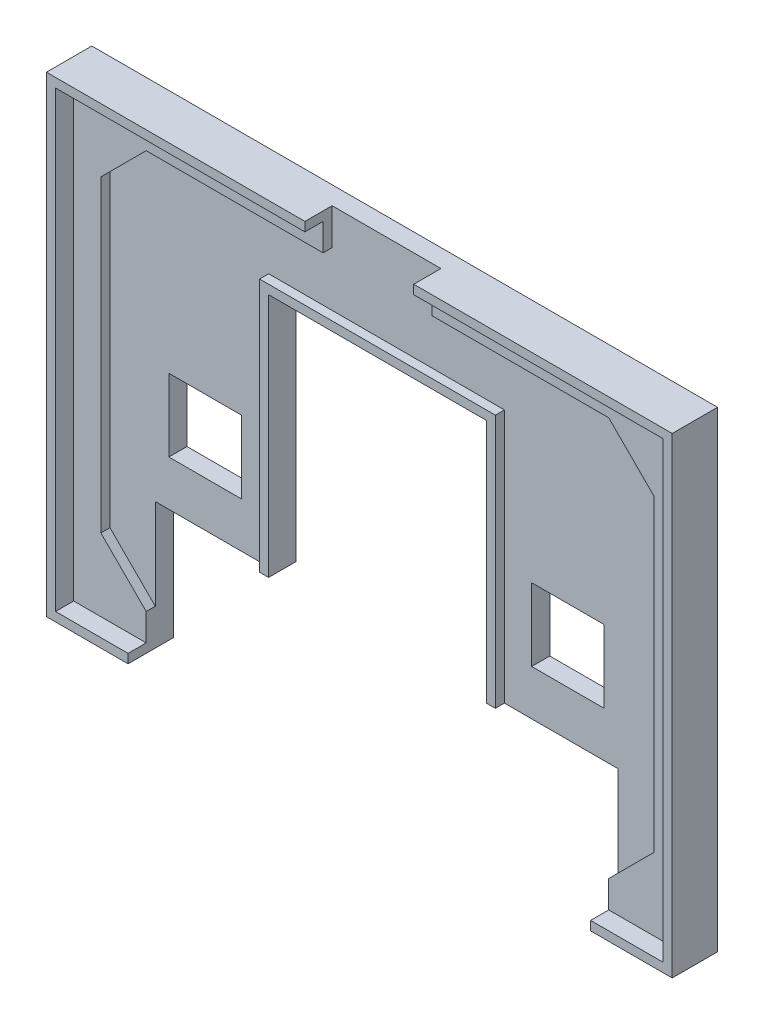
SolidWorks part; units mm, degrees
ref_plane "Přední rovina" through (0, 0, 0) normal (0, 0, 1) x (1, 0, 0)
ref_plane "Horní rovina" through (0, 0, 0) normal (0, 1, 0) x (1, 0, 0)
ref_plane "Pravá rovina" through (0, 0, 0) normal (1, 0, 0) x (0, 0, -1)
sketch "Skica1" plane through (0, 0, 0) normal (0, 0, 1) x (1, 0, 0)
  line L1 (-33.5, -25) -> (33.5, -25)
  line L2 (-33.5, -25) -> (-33.5, 25)
  line L3 (-33.5, 25) -> (33.5, 25)
  line L4 (33.5, -25) -> (33.5, 25)
  line L5 (-33.5, -25) -> (33.5, 25) construction
  line L6 (-33.5, 25) -> (33.5, -25) construction
  point P0 (0, 0)
  dimension "D1" = 67
  dimension "D2" = 50
extrude "Přidat vysunutím1" add sketch "Skica1" along normal blind 3
sketch "Skica2" plane through (0, 0, 3) normal (0, 0, 1) x (1, 0, 0)
  line L0 (-1000, 0) -> (49000, 0) construction
  line L1 (0, -1000) -> (0, 49000) construction
  line L2 (-1000, -22) -> (49000, -22) construction
  line L3 (-25.5, -1000) -> (-25.5, 49000) construction
  line L4 (-30.5, -1000) -> (-30.5, 49000) construction
  line L6 (-33.5, -25) -> (33.5, -25) construction
  line L7 (-25.5, -22) -> (-30.5, -17)
  line L8 (-30.5, -17) -> (-30.5, 17)
  line L9 (-25.5, -22) -> (25.5, -22)
  line L10 (30.5, -17) -> (30.5, 17)
  line L11 (25.5, -22) -> (30.5, -17)
  line L12 (25.5, 22) -> (30.5, 17)
  line L13 (-25.5, 22) -> (25.5, 22)
  line L14 (-25.5, 22) -> (-30.5, 17)
  point P20 (0, -22)
  point P21 (30.5, 0)
  point P24 (-30.5, 0)
  dimension "D1" = 30.5
  dimension "D2" = 5
  dimension "D3" = 3
  dimension "D4" = 45
extrude "Odebrat vysunutím1" cut sketch "Skica2" against normal offset from surface (1 mm away) 2 up to face at (0, 0, 0)
sketch "Skica3" plane through (0, 0, 0) normal (0, 0, -1) x (-1, 0, 0)
  line L0 (0, -1000) -> (0, 49000) construction
  line L1 (33.5, -25) -> (-33.5, -25) construction
  line L2 (24, 1) -> (16, 1)
  line L3 (24, 1) -> (24, -7)
  line L4 (24, -7) -> (16, -7)
  line L5 (16, 1) -> (16, -7)
  line L6 (-16, 1) -> (-16, -7)
  line L7 (33.5, -25) -> (-33.5, -25) construction
  line L8 (25.5, -25) -> (-25.5, -25)
  line L9 (25.5, -25) -> (25.5, -12)
  line L11 (-25.5, -25) -> (-25.5, -12)
  line L12 (-24, -7) -> (-16, -7)
  line L13 (25.5, -12) -> (12, -12)
  line L15 (12, -12) -> (12, 15)
  line L16 (12, 15) -> (-12, 15)
  line L17 (-12, -12) -> (-12, 15)
  line L18 (-12, -12) -> (-25.5, -12)
  line L19 (-24, 1) -> (-24, -7)
  line L20 (-24, 1) -> (-16, 1)
  dimension "D1" = 16
  dimension "D2" = 8
  dimension "D3" = 18
  dimension "D4" = 13
  dimension "D5" = 51
  dimension "D6" = 24
  dimension "D7" = 27
extrude "Odebrat vysunutím2" cut sketch "Skica3" against normal through all
sketch "Skica4" plane through (0, 0, 2) normal (0, 0, 1) x (1, 0, 0)
  line L0 (12, 15) -> (12, -12) construction
  line L1 (-12, -12) -> (-12, 15) construction
  line L2 (-12, 15) -> (12, 15) construction
  line L3 (12, 15) -> (12, -12)
  line L4 (-12, -12) -> (-12, 15)
  line L5 (-12, 15) -> (12, 15)
extrude "Vysunout tenkostěnný1" add sketch "Skica4" along normal up to surface (1 mm away) thin up to face at (0, -3.5714, 3) thin type one direction reverse wall 1
sketch "Skica5" plane through (0, 0, 0) normal (0, 0, -1) x (-1, 0, 0)
  line L0 (-33.5, 25) -> (33.5, 25) construction
  line L1 (33.5, 25) -> (33.5, -25) construction
  line L2 (33.5, -25) -> (25.5, -25) construction
  line L3 (-33.5, -25) -> (-33.5, 25) construction
  line L4 (-25.5, -25) -> (-33.5, -25) construction
  line L5 (-33.5, 25) -> (33.5, 25)
  line L6 (33.5, 25) -> (33.5, -25)
  line L7 (33.5, -25) -> (25.5, -25)
  line L8 (-33.5, -25) -> (-33.5, 25)
  line L9 (-25.5, -25) -> (-33.5, -25)
extrude "Vysunout tenkostěnný2" add sketch "Skica5" against normal blind 5 thin thin type one direction reverse wall 1
sketch "Skica6" plane through (0, 0, 2) normal (0, 0, 1) x (1, 0, 0)
  line L0 (0, -1000) -> (0, 49000) construction
  line L1 (25.5, 22) -> (-25.5, 22) construction
  line L2 (-6, 22) -> (6, 22)
  line L3 (-6, 22) -> (-6, 26)
  line L4 (-6, 26) -> (6, 26)
  line L5 (6, 22) -> (6, 26)
  line L6 (34.5, 26) -> (-34.5, 26) construction
  dimension "D1" = 12
extrude "Odebrat vysunutím3" cut sketch "Skica6" along normal through all
sketch "Skica8" plane through (0, 0, 0) normal (0, 0, -1) x (-1, 0, 0)
  line L0 (-28.7522, 22) -> (-27.75, 22)
  line L1 (-27.75, 22) -> (-27.75, 21)
  line L2 (-27.75, 21) -> (-26.75, 21)
  line L3 (-26.75, 21) -> (-26.75, 20)
  line L4 (-26.75, 20) -> (-25.75, 20)
  line L5 (-25.75, 20) -> (-25.75, 19)
  line L7 (-20.75, 19) -> (-20.75, 20)
  line L8 (-20.75, 20) -> (-19.75, 20)
  line L9 (-19.75, 20) -> (-19.75, 21)
  line L10 (-19.75, 21) -> (-18.75, 21)
  line L11 (-18.75, 21) -> (-18.75, 22)
  line L12 (-18.75, 22) -> (-17.75, 22)
  line L13 (-17.75, 22) -> (-17.75, 21)
  line L14 (-17.75, 21) -> (-16.75, 21)
  line L15 (-16.75, 21) -> (-16.75, 19)
  line L16 (-16.75, 19) -> (-15.75, 19)
  line L17 (-15.75, 19) -> (-15.75, 15)
  line L18 (-15.75, 15) -> (-14.75, 15)
  line L19 (-14.75, 15) -> (-14.75, 11)
  line L20 (-14.75, 11) -> (-15.75, 11)
  line L21 (-15.75, 11) -> (-15.75, 10)
  line L22 (-15.75, 10) -> (-16.75, 10)
  line L23 (-16.75, 10) -> (-16.75, 9)
  line L24 (-16.75, 9) -> (-17.75, 9)
  line L25 (-17.75, 9) -> (-17.75, 8)
  line L26 (-17.75, 8) -> (-18.75, 8)
  line L27 (-18.75, 8) -> (-18.75, 7)
  line L28 (-18.75, 7) -> (-27.7522, 7)
  line L29 (-27.7522, 7) -> (-27.7522, 8)
  line L30 (-27.7522, 8) -> (-28.7522, 8)
  line L31 (-28.7522, 8) -> (-28.7522, 9)
  line L32 (-28.7522, 9) -> (-29.7522, 9)
  line L33 (-29.7522, 9) -> (-29.7522, 10)
  line L34 (-29.7522, 10) -> (-30.7522, 10)
  line L35 (-30.7522, 10) -> (-30.7522, 11)
  line L36 (-30.7522, 11) -> (-31.7522, 11)
  line L37 (-31.7522, 11) -> (-31.7522, 15)
  line L38 (-31.7522, 15) -> (-30.7522, 15)
  line L39 (-30.7522, 15) -> (-30.7522, 19)
  line L40 (-30.7522, 19) -> (-29.7522, 19)
  line L41 (-29.7522, 19) -> (-29.7522, 21)
  line L42 (-29.7522, 21) -> (-28.7522, 21)
  line L43 (-28.7522, 21) -> (-28.7522, 22)
  line L44 (-25.75, 19) -> (-20.75, 19)
  line L45 (-12, 15) -> (-12, -12) construction
  line L47 (-34.5, 26) -> (34.5, 26) construction
  line L48 (0, 0) -> (0, 28.5236) construction
  line L49 (25.75, 19) -> (20.75, 19)
  line L50 (25.75, 20) -> (25.75, 19)
  line L51 (26.75, 20) -> (25.75, 20)
  line L52 (26.75, 21) -> (26.75, 20)
  line L53 (27.75, 21) -> (26.75, 21)
  line L54 (27.75, 22) -> (27.75, 21)
  line L55 (28.7522, 22) -> (27.75, 22)
  line L56 (28.7522, 21) -> (28.7522, 22)
  line L57 (29.7522, 21) -> (28.7522, 21)
  line L58 (29.7522, 19) -> (29.7522, 21)
  line L59 (30.7522, 19) -> (29.7522, 19)
  line L60 (30.7522, 15) -> (30.7522, 19)
  line L61 (31.7522, 15) -> (30.7522, 15)
  line L62 (31.7522, 11) -> (31.7522, 15)
  line L63 (30.7522, 11) -> (31.7522, 11)
  line L64 (30.7522, 10) -> (30.7522, 11)
  line L65 (29.7522, 10) -> (30.7522, 10)
  line L66 (29.7522, 9) -> (29.7522, 10)
  line L67 (28.7522, 9) -> (29.7522, 9)
  line L68 (28.7522, 8) -> (28.7522, 9)
  line L69 (27.7522, 8) -> (28.7522, 8)
  line L70 (27.7522, 7) -> (27.7522, 8)
  line L71 (18.75, 7) -> (27.7522, 7)
  line L72 (18.75, 8) -> (18.75, 7)
  line L73 (17.75, 8) -> (18.75, 8)
  line L74 (17.75, 9) -> (17.75, 8)
  line L75 (16.75, 9) -> (17.75, 9)
  line L76 (16.75, 10) -> (16.75, 9)
  line L77 (15.75, 10) -> (16.75, 10)
  line L78 (15.75, 11) -> (15.75, 10)
  line L79 (14.75, 11) -> (15.75, 11)
  line L80 (14.75, 15) -> (14.75, 11)
  line L81 (15.75, 15) -> (14.75, 15)
  line L82 (15.75, 19) -> (15.75, 15)
  line L83 (16.75, 19) -> (15.75, 19)
  line L84 (16.75, 21) -> (16.75, 19)
  line L85 (17.75, 21) -> (16.75, 21)
  line L86 (17.75, 22) -> (17.75, 21)
  line L87 (18.75, 22) -> (17.75, 22)
  line L88 (18.75, 21) -> (18.75, 22)
  line L89 (19.75, 21) -> (18.75, 21)
  line L90 (19.75, 20) -> (19.75, 21)
  line L91 (20.75, 20) -> (19.75, 20)
  line L92 (20.75, 19) -> (20.75, 20)
  dimension "D1" = 1.0022
  dimension "D2" = 1
  dimension "D3" = 1
  dimension "D4" = 1
  dimension "D5" = 1
  dimension "D6" = 1
  dimension "D7" = 1
  dimension "D8" = 1
  dimension "D9" = 1
  dimension "D10" = 1
  dimension "D11" = 1
  dimension "D12" = 1
  dimension "D13" = 1
  dimension "D14" = 1
  dimension "D15" = 1
  dimension "D16" = 1
  dimension "D17" = 1
  dimension "D18" = 1
  dimension "D19" = 2
  dimension "D20" = 5
  dimension "D21" = 4
  dimension "D22" = 4
  dimension "D23" = 4
  dimension "D24" = 4
  dimension "D25" = 1
  dimension "D26" = 1
  dimension "D27" = 1
  dimension "D28" = 1
  dimension "D29" = 1
  dimension "D30" = 1
  dimension "D31" = 1
  dimension "D32" = 1
  dimension "D33" = 1
  dimension "D34" = 1
  dimension "D35" = 1
  dimension "D36" = 1
  dimension "D37" = 1
  dimension "D38" = 1
  dimension "D39" = 1
  dimension "D40" = 1
  dimension "D41" = 1
  dimension "D42" = 2.75
  dimension "D43" = 4
extrude "Odebrat vysunutím4" cut sketch "Skica8" against normal blind 1
sketch "Skica9" plane through (0, 0, 0) normal (0, 0, -1) x (-1, 0, 0)
  line L0 (-30.7522, 15) -> (-31.7522, 15) construction
  line L1 (-27.75, 14) -> (-25.75, 14)
  line L2 (-27.75, 14) -> (-27.75, 12)
  line L3 (-27.75, 12) -> (-25.75, 12)
  line L4 (-25.75, 14) -> (-25.75, 12)
  line L5 (-21.75, 10) -> (-21.75, 9)
  line L6 (-23.25, 19) -> (-23.25, 4.92) construction
  line L7 (-20.75, 19) -> (-25.75, 19) construction
  line L8 (-18.75, 12) -> (-20.75, 12)
  line L9 (-20.75, 14) -> (-20.75, 12)
  line L10 (-18.75, 14) -> (-20.75, 14)
  line L11 (-18.75, 14) -> (-18.75, 12)
  line L12 (-23.75, 12) -> (-22.75, 12)
  line L13 (-22.75, 12) -> (-22.75, 10)
  line L14 (-22.75, 10) -> (-21.75, 10)
  line L15 (-21.75, 9) -> (-24.75, 9)
  line L16 (-24.75, 9) -> (-24.75, 10)
  line L17 (-24.75, 10) -> (-23.75, 10)
  line L18 (-23.75, 10) -> (-23.75, 12)
  line L19 (0, 0) -> (0, 33.5066) construction
  line L20 (-25.75, 19) -> (-25.75, 20) construction
  line L22 (24.75, 10) -> (23.75, 10)
  line L23 (24.75, 9) -> (24.75, 10)
  line L24 (21.75, 9) -> (24.75, 9)
  line L25 (21.75, 10) -> (21.75, 9)
  line L26 (22.75, 10) -> (21.75, 10)
  line L27 (22.75, 12) -> (22.75, 10)
  line L28 (23.75, 12) -> (22.75, 12)
  line L29 (23.75, 10) -> (23.75, 12)
  line L30 (18.75, 14) -> (18.75, 12)
  line L31 (18.75, 14) -> (20.75, 14)
  line L32 (20.75, 14) -> (20.75, 12)
  line L33 (18.75, 12) -> (20.75, 12)
  line L34 (27.75, 12) -> (25.75, 12)
  line L35 (25.75, 14) -> (25.75, 12)
  line L36 (27.75, 14) -> (25.75, 14)
  line L37 (27.75, 14) -> (27.75, 12)
  dimension "D1" = 2
  dimension "D2" = 3
  dimension "D3" = 1
  dimension "D4" = 1
  dimension "D5" = 1
  dimension "D6" = 2
  dimension "D7" = 2
  dimension "D8" = 1
  dimension "D9" = 2
  dimension "D10" = 0
extrude "Přidat vysunutím2" add sketch "Skica9" along normal blind 1 from offset 1 offset against normal yes
sketch "Skica11" plane through (0, 0, 0) normal (0, 0, -1) x (-1, 0, 0)
  line L0 (-21.75, 10) -> (-22.75, 10) construction
  line L1 (-21.75, 11) -> (-20.75, 11)
  line L2 (-21.75, 11) -> (-21.75, 10)
  line L3 (-21.75, 10) -> (-20.75, 10)
  line L4 (-20.75, 11) -> (-20.75, 10)
  line L5 (-21.75, 9) -> (-21.75, 10) construction
  line L6 (-23.2511, 7) -> (-23.2511, 16.4685) construction
  line L7 (-27.7522, 7) -> (-18.75, 7) construction
  line L8 (-24.7522, 10) -> (-25.7522, 10)
  line L9 (-25.7522, 11) -> (-25.7522, 10)
  line L10 (-24.7522, 11) -> (-25.7522, 11)
  line L11 (-24.7522, 11) -> (-24.7522, 10)
  line L12 (0, 0) -> (0, 34.7787) construction
  line L13 (21.75, 10) -> (20.75, 10)
  line L14 (20.75, 11) -> (20.75, 10)
  line L15 (21.75, 11) -> (20.75, 11)
  line L16 (21.75, 11) -> (21.75, 10)
  line L17 (24.7522, 11) -> (24.7522, 10)
  line L18 (24.7522, 11) -> (25.7522, 11)
  line L19 (25.7522, 11) -> (25.7522, 10)
  line L20 (24.7522, 10) -> (25.7522, 10)
  dimension "D1" = 1
  dimension "D2" = 1
  dimension "D3" = 0
  dimension "D4" = 0
extrude "Přidat vysunutím3" add sketch "Skica11" along normal blind 1 from offset 1 offset against normal yes
sketch "Skica12" plane through (0, 0, 0) normal (0, 0, -1) x (-1, 0, 0)
  line L0 (-11.1, 23.3) -> (-9.5, 23.3)
  line L1 (-9.5, 23.3) -> (-9.5, 20.9)
  line L2 (-9.5, 20.9) -> (-7.9, 20.9)
  line L3 (-7.9, 20.9) -> (-7.9, 23.3)
  line L4 (-7.9, 23.3) -> (-6.3, 23.3)
  line L5 (-6.3, 23.3) -> (-6.3, 17.7)
  line L6 (-6.3, 17.7) -> (-7.9, 17.7)
  line L7 (-7.9, 17.7) -> (-7.9, 20.1)
  line L8 (-7.9, 20.1) -> (-9.5, 20.1)
  line L9 (-9.5, 20.1) -> (-9.5, 17.7)
  line L10 (-9.5, 17.7) -> (-11.1, 17.7)
  line L11 (-11.1, 17.7) -> (-11.1, 23.3)
  line L12 (-1.3002, 23.3) -> (-4.5, 23.3)
  line L13 (-1.3002, 23.3) -> (-1.3002, 22.5)
  line L14 (-1.3002, 22.5) -> (-0.5002, 22.5)
  line L15 (-0.5002, 22.5) -> (-0.5002, 17.7)
  line L16 (-0.5002, 17.7) -> (-2.1002, 17.7)
  line L17 (-2.1002, 17.7) -> (-2.1002, 20.1)
  line L18 (-2.1002, 20.1) -> (-3.7, 20.1)
  line L19 (-3.7, 20.1) -> (-3.7, 17.7)
  line L20 (-3.7, 17.7) -> (-5.3, 17.7)
  line L21 (-5.3, 17.7) -> (-5.3, 22.5)
  line L22 (-5.3, 22.5) -> (-4.5, 22.5)
  line L23 (-4.5, 23.3) -> (-4.5, 22.5)
  line L24 (0.4998, 23.3) -> (5.2998, 23.3)
  line L25 (5.2998, 23.3) -> (5.2998, 22.1)
  line L26 (5.2998, 22.1) -> (2.0998, 22.1)
  line L27 (2.0998, 22.1) -> (2.0998, 20.9)
  line L28 (2.0998, 20.9) -> (4.4998, 20.9)
  line L29 (4.4998, 20.9) -> (4.4998, 19.7)
  line L30 (4.4998, 19.7) -> (2.0998, 19.7)
  line L31 (2.0998, 19.7) -> (2.0998, 17.7)
  line L32 (2.0998, 17.7) -> (0.4998, 17.7)
  line L33 (0.4998, 17.7) -> (0.4998, 23.3)
  line L34 (7.0998, 23.3) -> (10.2998, 23.3)
  line L35 (10.2998, 23.3) -> (10.2998, 22.5)
  line L36 (10.2998, 22.5) -> (11.0998, 22.5)
  line L41 (7.0998, 17.7) -> (7.0998, 18.5)
  line L42 (7.0998, 18.5) -> (6.2998, 18.5)
  line L43 (6.2998, 18.5) -> (6.2998, 22.5)
  line L44 (6.2998, 22.5) -> (7.0998, 22.5)
  line L45 (7.0998, 22.5) -> (7.0998, 23.3)
  line L47 (-34.5, 26) -> (34.5, 26) construction
  line L52 (7.0998, 17.7) -> (10.2998, 17.7)
  line L53 (10.2998, 17.7) -> (10.2998, 18.5)
  line L54 (10.2998, 18.5) -> (11.0998, 18.5)
  line L55 (11.0998, 18.5) -> (11.0998, 22.5)
  line L60 (-12, 15) -> (-12, -12) construction
  dimension "D2" = 5.6
  dimension "D3" = 5.6
  dimension "D4" = 2.7
  dimension "D5" = 1.6
  dimension "D6" = 1.6
  dimension "D7" = 1.6
  dimension "D8" = 1.6
  dimension "D9" = 0.8
  dimension "D10" = 2.4
  dimension "D11" = 2.7
  dimension "D12" = 1
  dimension "D13" = 1.6
  dimension "D14" = 1.6
  dimension "D15" = 1.5998
  dimension "D16" = 0.8
  dimension "D17" = 0.8
  dimension "D18" = 2.4
  dimension "D19" = 2.4
  dimension "D20" = 0.8
  dimension "D21" = 0.8
  dimension "D22" = 1
  dimension "D23" = 1.6
  dimension "D24" = 4.8
  dimension "D25" = 3.2
  dimension "D26" = 1.2
  dimension "D27" = 1.2
  dimension "D28" = 1.2
  dimension "D29" = 3.2
  dimension "D30" = 0.8
  dimension "D31" = 0.8
  dimension "D32" = 0.8
  dimension "D33" = 0.8
  dimension "D34" = 0.8
  dimension "D35" = 0.8
  dimension "D36" = 0.8
  dimension "D37" = 0.8
  dimension "D38" = 5.6
  dimension "D39" = 1
  dimension "D40" = 2.4
  dimension "0,9" = 0.9
extrude "Odebrat vysunutím5" cut sketch "Skica12" against normal blind 1
sketch "Skica13" plane through (0, 0, 0) normal (0, 0, -1) x (-1, 0, 0)
  line L0 (-5.3, 22.5) -> (-5.3, 17.7) construction
  line L1 (-3.7, 22.5) -> (-2.1002, 22.5)
  line L2 (-3.7, 22.5) -> (-3.7, 20.9)
  line L3 (-3.7, 20.9) -> (-2.1002, 20.9)
  line L4 (-2.1002, 22.5) -> (-2.1002, 20.9)
  line L5 (-0.5002, 17.7) -> (-0.5002, 22.5) construction
  line L6 (-1.3002, 23.3) -> (-4.5, 23.3) construction
  line L7 (-3.7, 20.1) -> (-2.1002, 20.1) construction
  line L8 (10.2998, 23.3) -> (7.0998, 23.3) construction
  line L9 (7.8998, 21.7) -> (9.4998, 21.7)
  line L10 (7.8998, 21.7) -> (7.8998, 19.3)
  line L11 (7.8998, 19.3) -> (9.4998, 19.3)
  line L12 (9.4998, 21.7) -> (9.4998, 19.3)
  line L13 (7.0998, 17.7) -> (10.2998, 17.7) construction
  line L14 (11.0998, 18.5) -> (11.0998, 22.5) construction
  line L15 (6.2998, 22.5) -> (6.2998, 18.5) construction
  dimension "D1" = 1.6
  dimension "D2" = 1.6
  dimension "D3" = 0.8
  dimension "D4" = 0.8
  dimension "D5" = 1.6
  dimension "D6" = 1.6
  dimension "D7" = 1.6
  dimension "D8" = 1.6
extrude "Přidat vysunutím4" add sketch "Skica13" along normal blind 1 from offset 1 offset against normal yes
